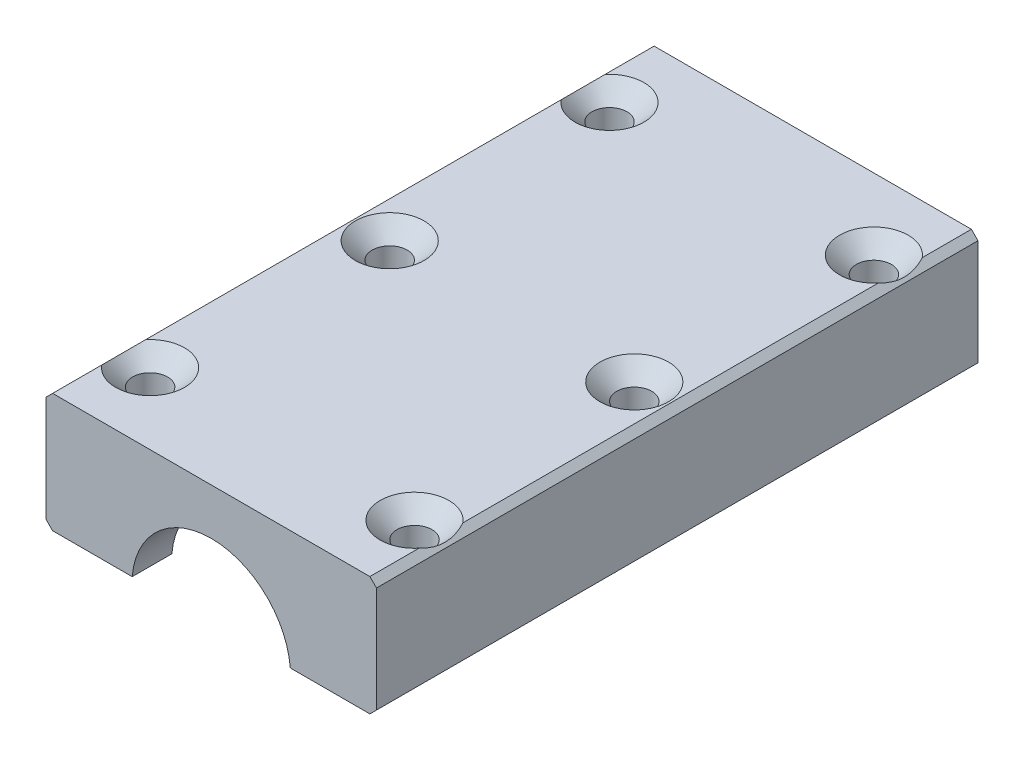
SolidWorks part; units mm, degrees
material "Латунь"
ref_plane "Front Plane" through (0, 0, 0) normal (0, 0, 1) x (1, 0, 0)
ref_plane "Top Plane" through (0, 0, 0) normal (0, 1, 0) x (1, 0, 0)
ref_plane "Right Plane" through (0, 0, 0) normal (1, 0, 0) x (0, 0, -1)
sketch "Sketch1" plane through (0, 0, 0) normal (0, 0, 1) x (1, 0, 0)
  line L0 (11.9583, 1) -> (25, 1)
  line L1 (-25, 1) -> (-11.9583, 1)
  line L2 (-25, 1) -> (-25, 19)
  line L3 (-25, 19) -> (25, 19)
  line L4 (25, 1) -> (25, 19)
  arc A0 (11.9583, 1) -> (-11.9583, 1) centre (0, 0) ccw
  point P7 (11.8929, 1.6)
  point P8 (-25, 1)
  point P9 (25, 1.6667)
  dimension "D1" = 50
  dimension "D2" = 12
  dimension "D3" = 18
  dimension "D4" = 1
extrude "Boss-Extrude1" add sketch "Sketch1" against normal blind 91
chamfer "Chamfer1" distance 1 distance2 1 4 edges at (-25, 1, -45.5) (-25, 19, -45.5) (25, 19, -45.5) (25, 1, -45.5)
ref_plane "Plane1" through (0, 0, 0) normal (0, -1, 0) x (-1, 0, 0)
sketch "Sketch2" plane through (0, 0, 0) normal (0, -1, 0) x (1, 0, 0)
  line L1 (8.4751, -6) -> (15, -6)
  line L2 (8.4751, -6) -> (8.4751, -24.5)
  line L3 (8.4751, -24.5) -> (15, -24.5)
  line L4 (15, -6) -> (15, -24.5)
  line L6 (9.8647, -85) -> (15, -85)
  line L7 (9.8647, -85) -> (9.8647, -75.5)
  line L8 (9.8647, -75.5) -> (15, -75.5)
  line L9 (15, -85) -> (15, -75.5)
  line L11 (0, 0) -> (0, -96.9635) construction
  line L12 (11.9583, 0) -> (24, 0) construction
  dimension "D1" = 6
  dimension "D2" = 18.5
  dimension "D3" = 51
  dimension "D4" = 9.5
revolve "Cut-Revolve2" cut sketch "Sketch2" angle 360 about L11
ref_plane "Plane2" through (0, 19, 0) normal (0, 1, 0) x (1, 0, 0)
sketch "Sketch3" plane through (0, 19, 0) normal (0, -1, 0) x (1, 0, 0)
  line L0 (-20, -10.75) -> (20, -10.75) construction
  line L3 (-20, -80.25) -> (20, -80.25) construction
  line L10 (-18.5, -45.5) -> (18.5, -45.5) construction
  line L23 (0, 0) -> (0, -96.9635) construction
  point P12 (0, -80.25)
  point P13 (0, -45.5)
  point P28 (20, -10.75)
  point P29 (18.5, -45.5)
  point P30 (20, -80.25)
  point P31 (-20, -80.25)
  point P32 (-18.5, -45.5)
  point P33 (-20, -10.75)
  point P34 (0, -10.75)
hole_wizard "Зенковка для  винта с плоской головкой M51" positions "Sketch7" profile "Sketch6" countersink size "M5" standard "Ansi Metric" end condition through all
sketch "Sketch7" plane through (0, 19, 0) normal (0, 1, 0) x (1, 0, 0)
  point P0 (-20, 80.25)
  point P3 (20, 80.25)
  point P6 (18.5, 45.5)
  point P9 (-18.5, 45.5)
  point P12 (-20, 10.75)
  point P15 (20, 10.75)
sketch "Sketch6" plane through (-20, 19, -80.25) normal (1, 0, 0) x (0, 0, 1)
  line L0 (0, 0) -> (0, 18)
  line L1 (0, 18) -> (2.65, 18)
  line L2 (2.65, 18) -> (2.65, 2.55)
  line L3 (2.65, 2.55) -> (5.2, 0)
  line L5 (5.2, 0) -> (0, 0)
  line L6 (-2.65, 2.55) -> (-5.2, 0) construction
  line L11 (0, -6.35) -> (0, 107.95) construction
  dimension "Thru Hole Dia." = 5.3
  dimension "Thru Hole Depth" = 18
  dimension "Near C'Sink Dia." = 10.4
  dimension "Near C'Sink Angle" = 90
